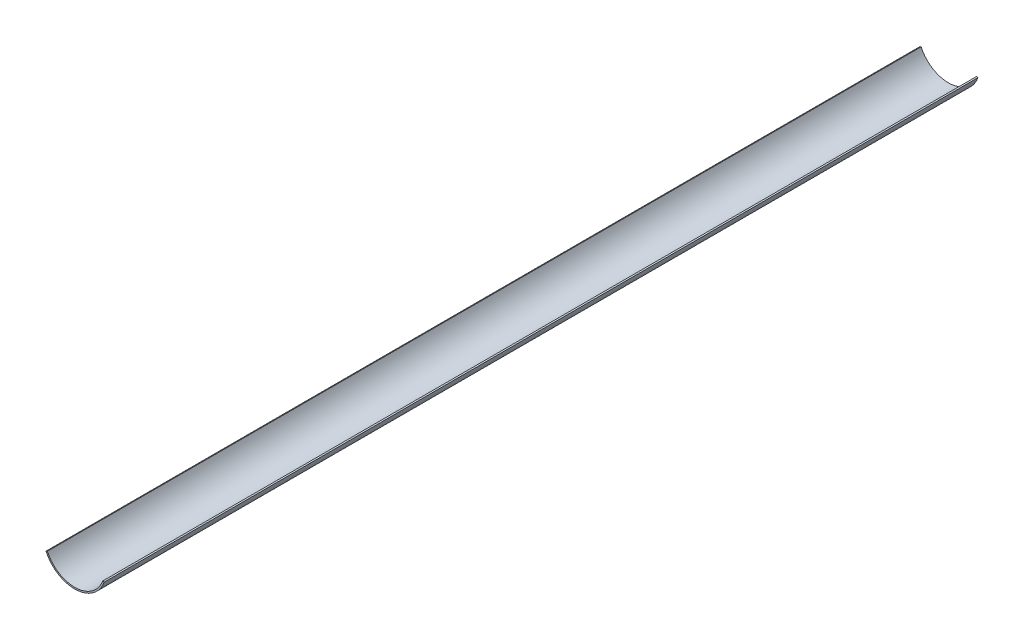
SolidWorks part; units mm, degrees
material "Plain Carbon Steel"
ref_plane "Front Plane" through (0, 0, 0) normal (0, 0, 1) x (1, 0, 0)
ref_plane "Top Plane" through (0, 0, 0) normal (0, 1, 0) x (1, 0, 0)
ref_plane "Right Plane" through (0, 0, 0) normal (1, 0, 0) x (0, 0, -1)
sketch "Sketch1" plane through (0, 0, 0) normal (0, 0, 1) x (1, 0, 0)
  line L0 (-5.4644, -2.478) -> (-5.74, -2.5965)
  line L1 (5.6254, -2.0868) -> (5.9276, -2.1338)
  arc A0 (5.6254, -2.0868) -> (-5.4644, -2.478) centre (0, 0) cw
  arc A1 (-5.74, -2.5965) -> (5.9276, -2.1338) centre (0, 0) ccw
  dimension "D1" = 6
  dimension "D2" = 0.3
extrude "Boss-Extrude1" add sketch "Sketch1" along normal blind 175
